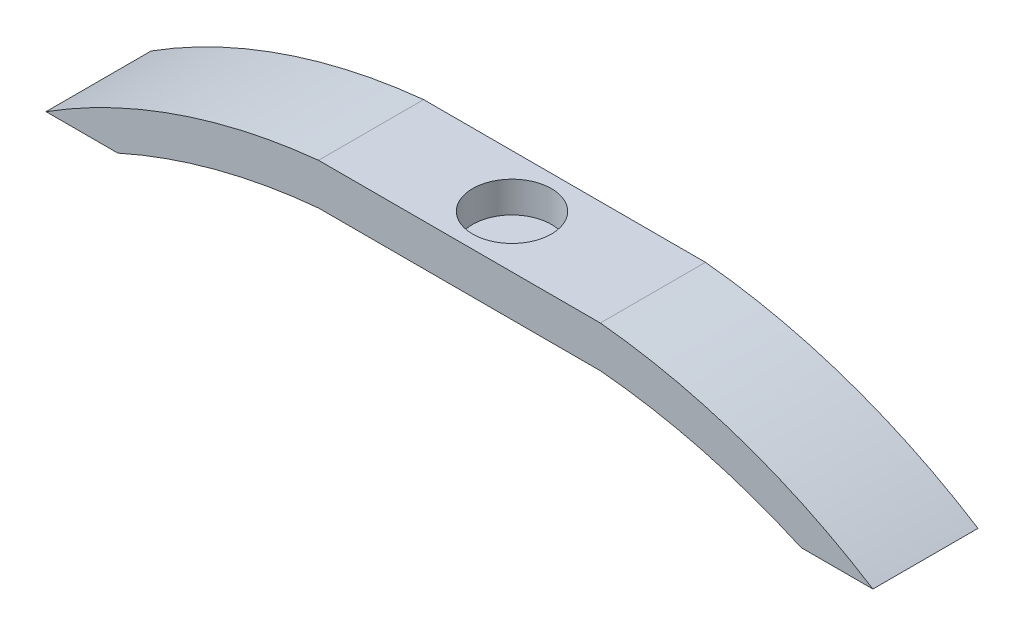
SolidWorks part; units mm, degrees
ref_plane "Front Plane" through (0, 0, 0) normal (0, 0, 1) x (1, 0, 0)
ref_plane "Top Plane" through (0, 0, 0) normal (0, 1, 0) x (1, 0, 0)
ref_plane "Right Plane" through (0, 0, 0) normal (1, 0, 0) x (0, 0, -1)
sketch "Sketch1" plane through (0, 0, 0) normal (0, 1, 0) x (1, 0, 0)
  line L1 (-7.62, 5.08) -> (7.62, 5.08)
  line L2 (-7.62, 5.08) -> (-7.62, -5.08)
  line L3 (-7.62, -5.08) -> (7.62, -5.08)
  line L4 (7.62, 5.08) -> (7.62, -5.08)
  line L5 (-7.62, 5.08) -> (7.62, -5.08) construction
  line L6 (-7.62, -5.08) -> (7.62, 5.08) construction
  point P0 (0, 0)
  dimension "D1" = 15.24
  dimension "D2" = 10.16
extrude "Boss-Extrude1" add sketch "Sketch1" along normal blind 4
sketch "Sketch2" plane through (0, 0, 5.08) normal (0, 0, 1) x (1, 0, 0)
  line L0 (0, 4) -> (0, -5.1)
  line L1 (7.62, 4) -> (13.62, 4)
  line L2 (0, 4) -> (13.62, 4)
  line L3 (-7.62, 4) -> (7.62, 4) construction
  line L5 (7.62, 0) -> (13.62, 0)
  line L9 (7.62, 4) -> (7.62, 0)
  line L10 (-7.62, 4) -> (-7.62, 0)
  line L11 (39.965, -5.1) -> (33.025, -5.1)
  line L12 (-39.965, -5.1) -> (-33.025, -5.1)
  line L13 (-7.62, 0) -> (-13.62, 0)
  line L14 (-7.62, 4) -> (-13.62, 4)
  line L15 (-7.62, 4) -> (-7.62, 0)
  arc A11 (39.965, -5.1) -> (13.62, 4) centre (7.5477, -56.2648) ccw
  arc A12 (33.025, -5.1) -> (13.62, 0) centre (8.1391, -60.3215) ccw
  arc A13 (-33.025, -5.1) -> (-13.62, 0) centre (-8.1391, -60.3215) cw
  arc A14 (-39.965, -5.1) -> (-13.62, 4) centre (-7.5477, -56.2648) cw
  dimension "D1" = 6
  dimension "D4" = 9.1
  dimension "D2" = 6.94
  dimension "D5" = 121.14
  dimension "D3" = 121.14
extrude "Boss-Extrude2" add sketch "Sketch2" along direction (0, 0, 1) on the side against the normal up to surface (10.16 mm away)
sketch "Sketch3" plane through (0, 4, 0) normal (0, 1, 0) x (1, 0, 0)
  circle A0 centre (0, 0) radius 3.81
  dimension "D1" = 7.62
extrude "Cut-Extrude1" cut sketch "Sketch3" against normal blind 3
